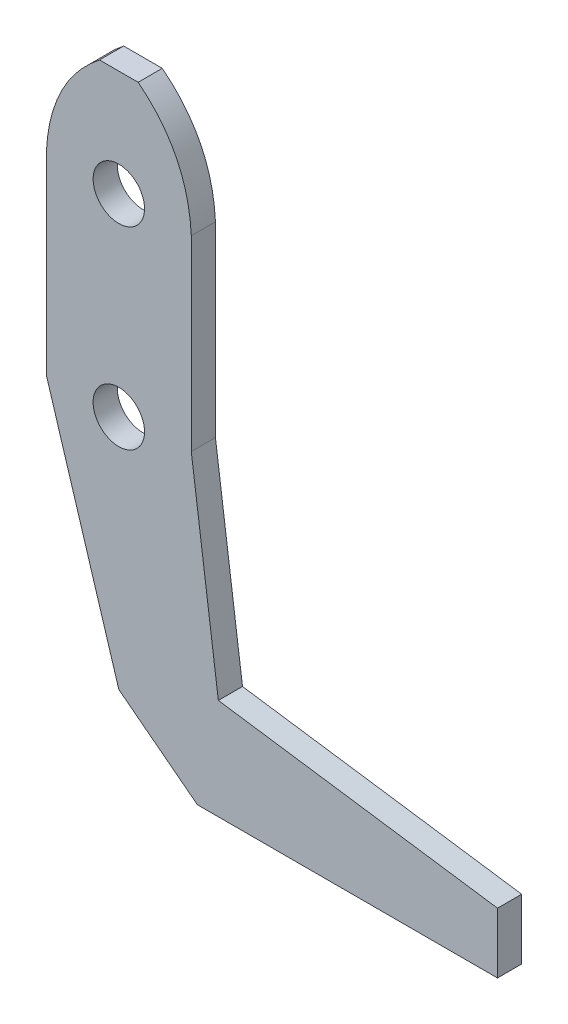
SolidWorks part; units mm, degrees
ref_plane "Front Plane" through (0, 0, 0) normal (0, 0, 1) x (1, 0, 0)
ref_plane "Top Plane" through (0, 0, 0) normal (0, 1, 0) x (1, 0, 0)
ref_plane "Right Plane" through (0, 0, 0) normal (1, 0, 0) x (0, 0, -1)
sketch "Sketch1" plane through (0, 0, 0) normal (0, 0, 1) x (1, 0, 0)
  line L0 (-2.54, 39.37) -> (2.54, 39.37)
  line L14 (10.327, -38.9756) -> (49.7728, -38.9756)
  line L17 (-9.525, 0) -> (0, -31.0256)
  line L18 (0, -31.0256) -> (10.327, -38.9756)
  line L19 (49.7728, -38.9756) -> (49.7728, -31.0256)
  line L20 (49.7728, -31.0256) -> (13.0807, -25.7257)
  line L21 (13.0807, -25.7257) -> (9.525, 0.8331)
  line L23 (-9.525, 25.4) -> (-9.525, 0)
  line L25 (9.525, 25.4) -> (9.525, 0.8331)
  line L26 (-9.525, 25.4) -> (9.525, 25.4) construction
  line L27 (0, -55) -> (0, 55) construction
  circle A0 centre (0, 25.4) radius 3.3782
  circle A1 centre (0, 0) radius 3.3782
  spline S0 degree 2 poles (-2.54, 39.37) (-9.0954, 34.2016) (-9.525, 25.4) knots 0 0 0 1 1 1
  spline S1 degree 2 poles (2.54, 39.37) (9.0954, 34.2016) (9.525, 25.4) knots 0 0 0 1 1 1
  point P6 (0, 39.37)
  point P20 (0, 25.4)
  point P21 (0, 39.37)
  dimension "D1" = 6.7564
  dimension "D7" = 5.08
  dimension "D2" = 25.4
  dimension "D3" = 39.37
  dimension "D6" = 19.05
extrude "Boss-Extrude1" add sketch "Sketch1" along normal blind 3.175
scale "Scale1" scale about centroid uniform scaling yes scale factor 0.35
